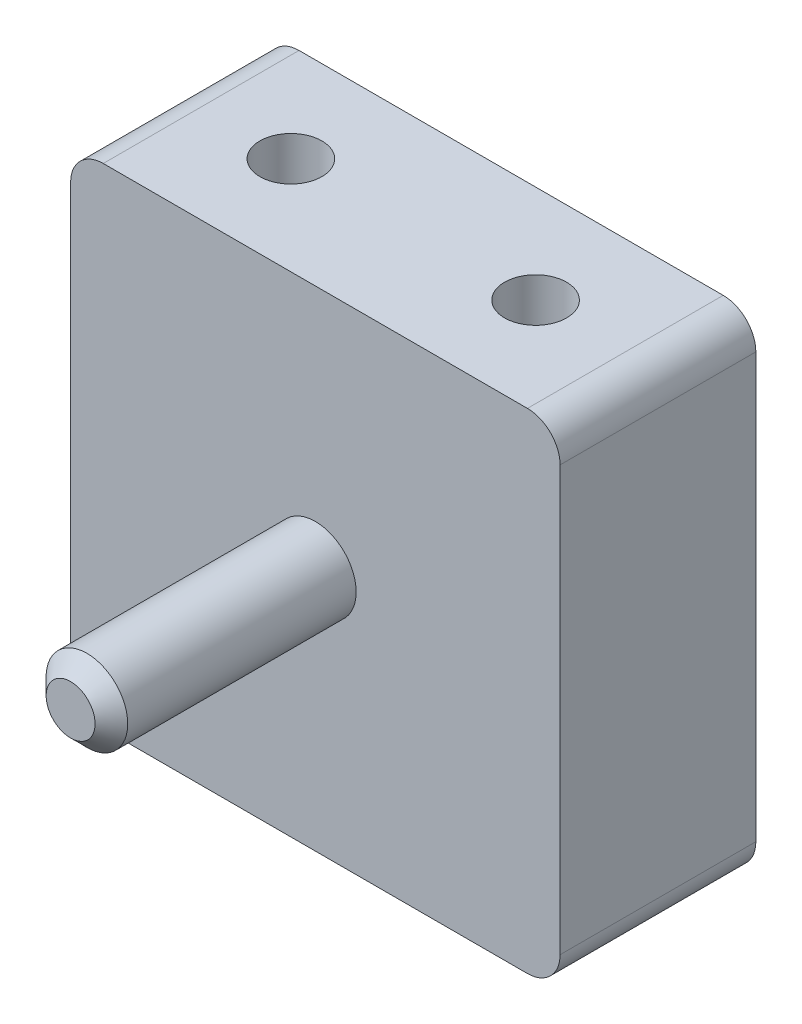
SolidWorks part; units mm, degrees
ref_plane "Front Plane" through (0, 0, 0) normal (0, 0, 1) x (1, 0, 0)
ref_plane "Top Plane" through (0, 0, 0) normal (0, 1, 0) x (1, 0, 0)
ref_plane "Right Plane" through (0, 0, 0) normal (1, 0, 0) x (0, 0, -1)
sketch "Sketch1" plane through (0, 0, 0) normal (0, 0, 1) x (1, 0, 0)
  line L1 (19.05, -19.05) -> (-19.05, -19.05)
  line L2 (19.05, -19.05) -> (19.05, 19.05)
  line L3 (19.05, 19.05) -> (-19.05, 19.05)
  line L4 (-19.05, -19.05) -> (-19.05, 19.05)
  line L5 (19.05, -19.05) -> (-19.05, 19.05) construction
  line L6 (19.05, 19.05) -> (-19.05, -19.05) construction
  circle A1 centre (0, 0) radius 1.5875
  point P0 (0, 0)
  dimension "D3" = 3.175
  dimension "D1" = 38.1
  dimension "D2" = 38.1
extrude "Boss-Extrude2" add sketch "Sketch1" along normal blind 15.24
sketch "Sketch3" plane through (0, 0, 15.24) normal (0, 0, 1) x (1, 0, 0)
  line L4 (-19.05, 19.05) -> (-19.05, -19.05)
  line L5 (-19.05, -19.05) -> (19.05, -19.05)
  line L6 (19.05, -19.05) -> (19.05, 19.05)
  line L7 (19.05, 19.05) -> (-19.05, 19.05)
  line L8 (-19.05, 19.05) -> (-19.05, -19.05)
  line L9 (-19.05, -19.05) -> (19.05, -19.05)
  line L10 (19.05, -19.05) -> (19.05, 19.05)
  line L11 (19.05, 19.05) -> (-19.05, 19.05)
  circle A0 centre (0, 0) radius 3.175
  dimension "D2" = 6.35
  dimension "D1" = 0
extrude "Boss-Extrude3" add sketch "Sketch3" along normal blind 19.05 contours A0
fillet "Fillet2" radius 2.54 4 edges at (-19.05, -19.05, 7.62) (19.05, -19.05, 7.62) (19.05, 19.05, 7.62) (-19.05, 19.05, 7.62)
chamfer "Chamfer1" distance 1.27 angle 45 1 edges at (3.175, 0, 34.29)
sketch "Sketch4" plane through (0, -19.05, 0) normal (0, -1, 0) x (1, 0, 0)
  line L0 (19.05, 15.24) -> (16.51, 15.24) construction
  line L1 (16.51, 0) -> (19.05, 0) construction
  line L2 (19.05, 0) -> (19.05, 15.24) construction
  line L3 (-16.51, 15.24) -> (-19.05, 15.24) construction
  line L4 (-19.05, 15.24) -> (-19.05, 0) construction
  line L5 (-19.05, 0) -> (-16.51, 0) construction
  line L6 (16.51, 15.24) -> (-16.51, 15.24) construction
  line L7 (-16.51, 0) -> (16.51, 0) construction
  line L8 (19.05, 15.24) -> (16.51, 15.24)
  line L9 (16.51, 0) -> (19.05, 0)
  line L10 (19.05, 0) -> (19.05, 15.24)
  line L11 (-16.51, 15.24) -> (-19.05, 15.24)
  line L12 (-19.05, 15.24) -> (-19.05, 0)
  line L13 (-19.05, 0) -> (-16.51, 0)
  line L14 (16.51, 15.24) -> (-16.51, 15.24)
  line L15 (-16.51, 0) -> (16.51, 0)
  line L16 (0, 15.24) -> (0, 0) construction
  line L17 (0, 7.62) -> (-9.525, 7.62) construction
  line L18 (0, 7.62) -> (9.525, 7.62) construction
  circle A0 centre (-9.525, 7.62) radius 2.413
  circle A1 centre (9.525, 7.62) radius 2.413
  dimension "D3" = 4.826
  dimension "D1" = 7.62
  dimension "D2" = 7.62
  dimension "D4" = 9.525
extrude "Cut-Extrude2" cut sketch "Sketch4" against normal blind 7.62 contours A0 | A1
sketch "Sketch5" plane through (0, 19.05, 0) normal (0, 1, 0) x (1, 0, 0)
  line L0 (-19.05, -15.24) -> (-16.51, -15.24) construction
  line L1 (-16.51, 0) -> (-19.05, 0) construction
  line L2 (-19.05, 0) -> (-19.05, -15.24) construction
  line L3 (16.51, -15.24) -> (19.05, -15.24) construction
  line L4 (19.05, -15.24) -> (19.05, 0) construction
  line L5 (19.05, 0) -> (16.51, 0) construction
  line L6 (-16.51, -15.24) -> (16.51, -15.24) construction
  line L7 (16.51, 0) -> (-16.51, 0) construction
  line L8 (-19.05, -15.24) -> (-16.51, -15.24)
  line L9 (-16.51, 0) -> (-19.05, 0)
  line L10 (-19.05, 0) -> (-19.05, -15.24)
  line L11 (16.51, -15.24) -> (19.05, -15.24)
  line L12 (19.05, -15.24) -> (19.05, 0)
  line L13 (19.05, 0) -> (16.51, 0)
  line L14 (-16.51, -15.24) -> (16.51, -15.24)
  line L15 (16.51, 0) -> (-16.51, 0)
  line L16 (0, 0) -> (0, -15.24) construction
  line L17 (0, -7.62) -> (-9.525, -7.62) construction
  line L18 (0, -7.62) -> (9.525, -7.62) construction
  circle A0 centre (9.525, -7.62) radius 2.413
  circle A1 centre (-9.525, -7.62) radius 2.413
  dimension "D5" = 4.826
  dimension "D1" = 7.62
  dimension "D2" = 7.62
  dimension "D3" = 9.525
extrude "Cut-Extrude3" cut sketch "Sketch5" against normal blind 7.62 contours A0 | A1
